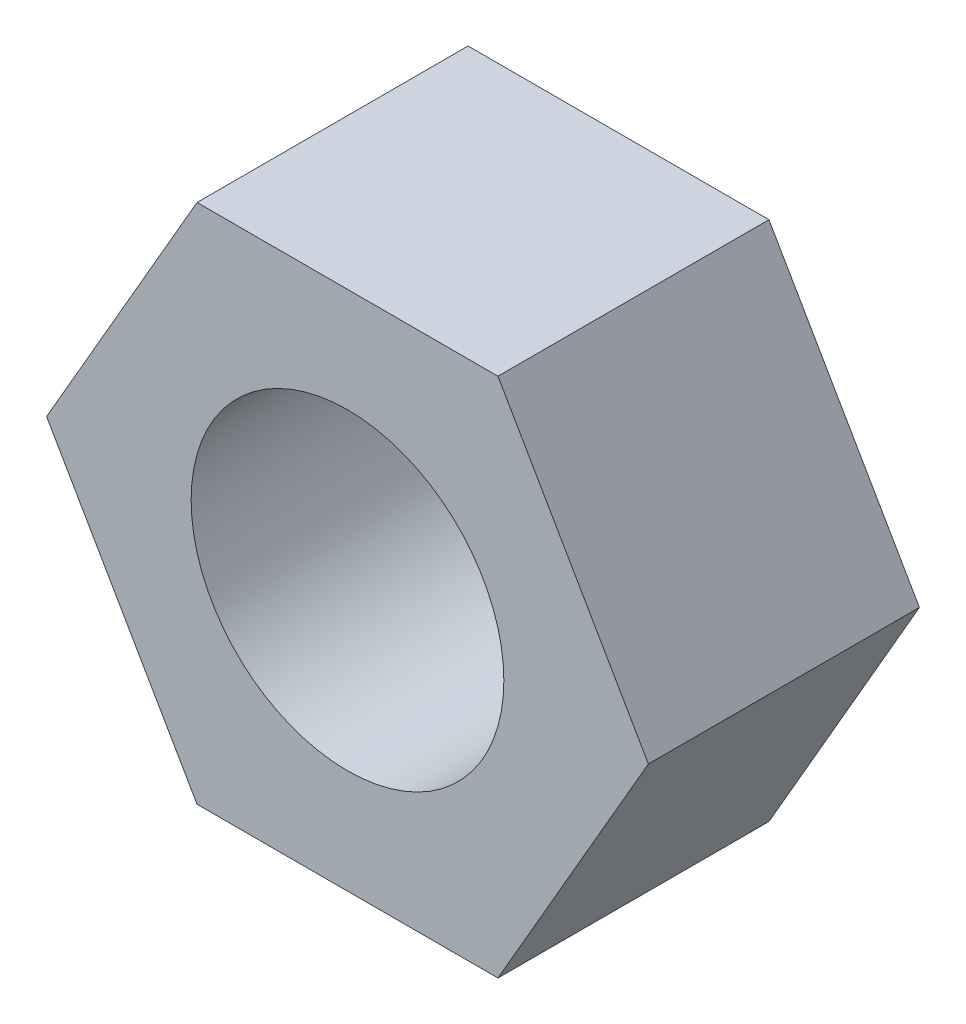
SolidWorks part; units mm, degrees
ref_plane "Front Plane" through (0, 0, 0) normal (0, 0, 1) x (1, 0, 0)
ref_plane "Top Plane" through (0, 0, 0) normal (0, 1, 0) x (1, 0, 0)
ref_plane "Right Plane" through (0, 0, 0) normal (1, 0, 0) x (0, 0, -1)
sketch "Sketch1" plane through (0, 0, 0) normal (0, 0, 1) x (1, 0, 0)
  line L1 (5.7735, 0) -> (2.8868, 5)
  line L2 (2.8868, 5) -> (-2.8868, 5)
  line L3 (-2.8868, 5) -> (-5.7735, 0)
  line L4 (-5.7735, 0) -> (-2.8868, -5)
  line L5 (-2.8868, -5) -> (2.8868, -5)
  line L6 (2.8868, -5) -> (5.7735, 0)
  circle A0 centre (0, 0) radius 5 construction
  dimension "D1" = 10
extrude "Boss-Extrude1" add sketch "Sketch1" along normal mid plane 5.2
sketch "Sketch2" plane through (0, 0, 2.6) normal (0, 0, 1) x (1, 0, 0)
  circle A0 centre (0, 0) radius 3
  dimension "D1" = 6
extrude "Cut-Extrude1" cut sketch "Sketch2" against normal through all
